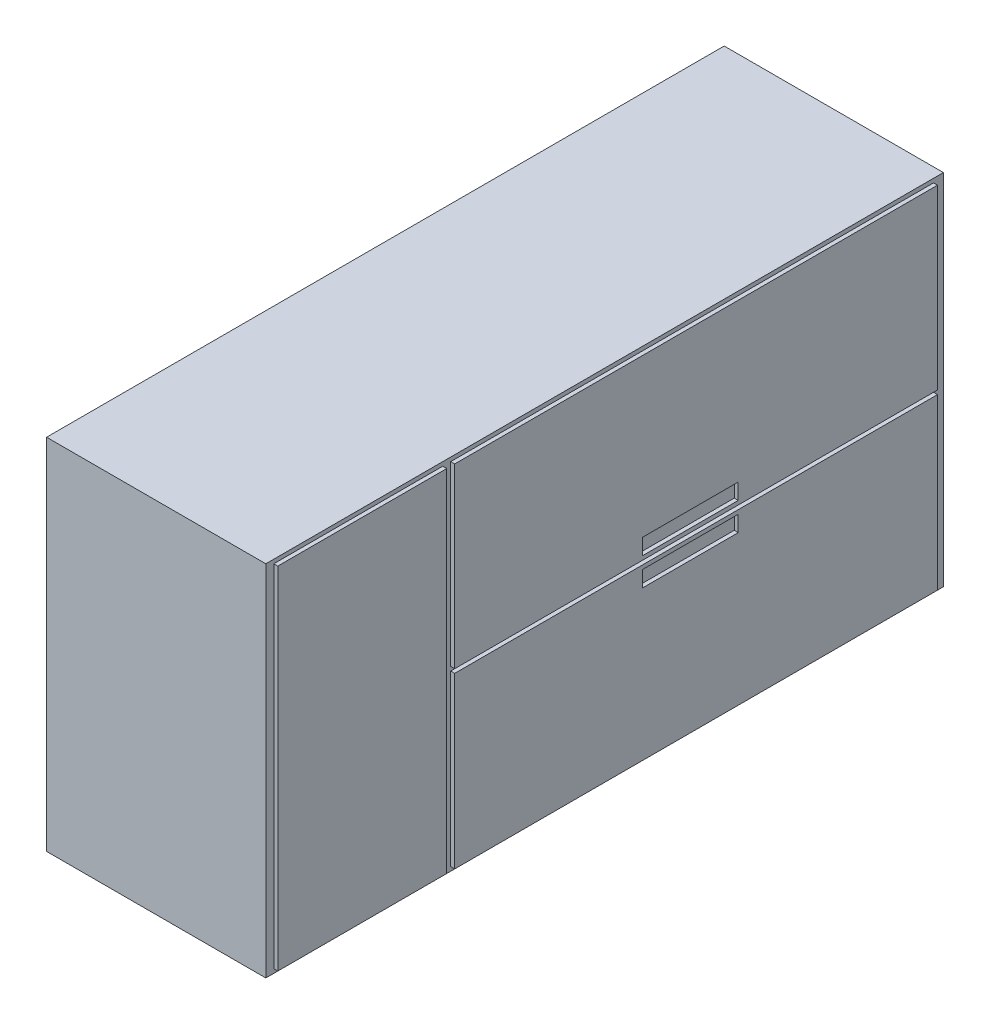
SolidWorks part; units mm, degrees
ref_plane "Front Plane" through (0, 0, 0) normal (0, 0, 1) x (1, 0, 0)
ref_plane "Top Plane" through (0, 0, 0) normal (0, 1, 0) x (1, 0, 0)
ref_plane "Right Plane" through (0, 0, 0) normal (1, 0, 0) x (0, 0, -1)
sketch "Sketch1" plane through (0, 0, 0) normal (0, 0, 1) x (1, 0, 0)
  line L1 (0, 0) -> (-550, 0)
  line L2 (0, 0) -> (0, -900)
  line L3 (0, -900) -> (-550, -900)
  line L4 (-550, 0) -> (-550, -900)
  dimension "D1" = 550
  dimension "D2" = 900
extrude "Boss-Extrude1" add sketch "Sketch1" along normal blind 1700
sketch "Sketch2" plane through (0, 0, 0) normal (1, 0, 0) x (0, 0, -1)
  line L0 (-1700, 0) -> (0, 0) construction
  line L1 (-1256.091, -10) -> (-1680, -10)
  line L2 (-1256.091, -10) -> (-1256.091, -890)
  line L3 (-1256.091, -890) -> (-1680, -890)
  line L4 (-1680, -10) -> (-1680, -890)
  line L5 (-1236.091, -10) -> (-24.7668, -10)
  line L6 (-1236.091, -10) -> (-1236.091, -455)
  line L7 (-1236.091, -455) -> (-24.7668, -455)
  line L8 (-24.7668, -10) -> (-24.7668, -455)
  line L9 (-1236.091, -465) -> (-24.7668, -465)
  line L10 (-1236.091, -465) -> (-1236.091, -890)
  line L11 (-1236.091, -890) -> (-24.7668, -890)
  line L12 (-24.7668, -465) -> (-24.7668, -890)
  line L13 (-1700, -900) -> (0, -900) construction
  line L14 (-1700, -900) -> (-1700, 0) construction
  line L15 (-764.7259, -475) -> (-524.7259, -475)
  line L16 (-764.7259, -475) -> (-764.7259, -515)
  line L17 (-764.7259, -515) -> (-524.7259, -515)
  line L18 (-524.7259, -475) -> (-524.7259, -515)
  line L19 (-764.7259, -445) -> (-524.7259, -445)
  line L20 (-764.7259, -445) -> (-764.7259, -405)
  line L21 (-764.7259, -405) -> (-524.7259, -405)
  line L22 (-524.7259, -445) -> (-524.7259, -405)
  dimension "D1" = 10
  dimension "D2" = 10
  dimension "D3" = 10
  dimension "D4" = 435
  dimension "D5" = 40
  dimension "D6" = 240
  dimension "D7" = 40
  dimension "D8" = 10
  dimension "D9" = 10
  dimension "D10" = 20
  dimension "D11" = 20
extrude "Boss-Extrude2" add sketch "Sketch2" along normal blind 10
